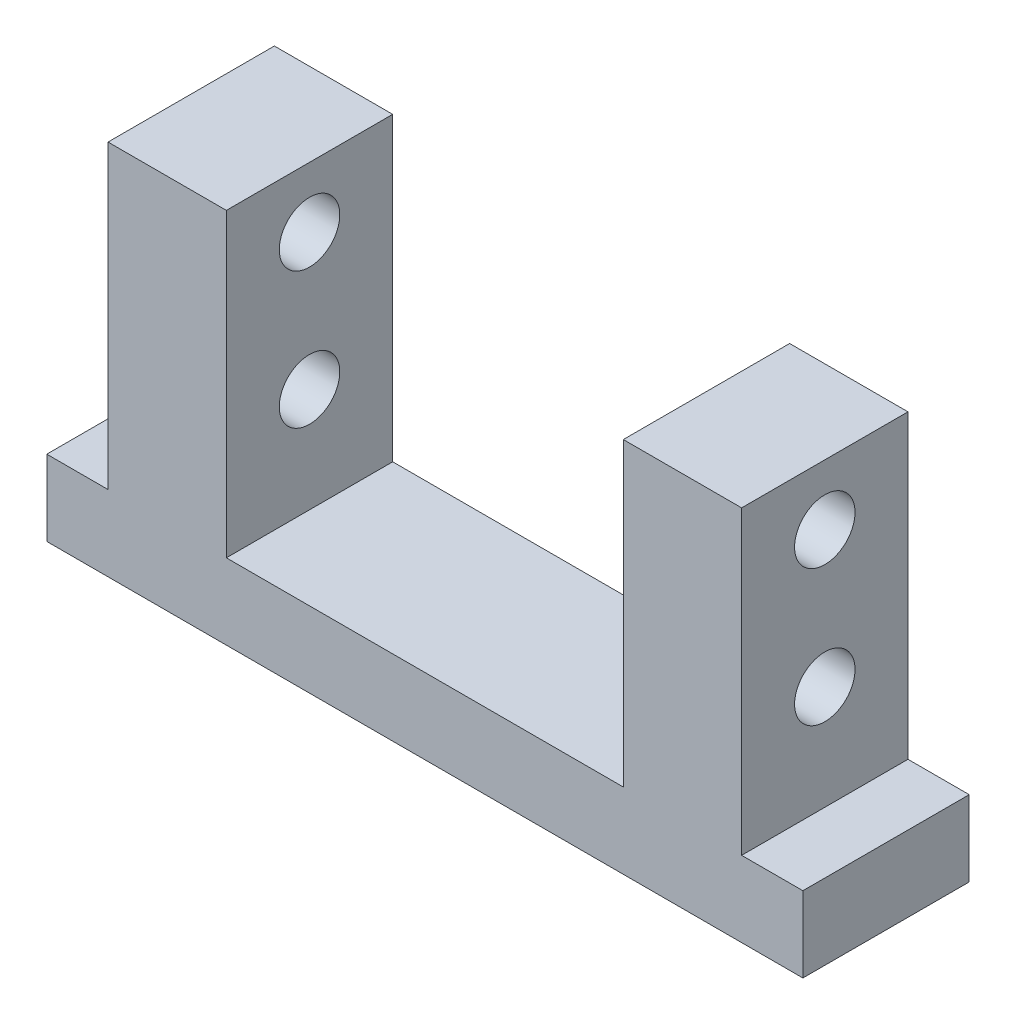
SolidWorks part; units mm, degrees
ref_plane "Front Plane" through (0, 0, 0) normal (0, 0, 1) x (1, 0, 0)
ref_plane "Top Plane" through (0, 0, 0) normal (0, 1, 0) x (1, 0, 0)
ref_plane "Right Plane" through (0, 0, 0) normal (1, 0, 0) x (0, 0, -1)
sketch "Sketch1" plane through (0, 0, 0) normal (0, 1, 0) x (1, 0, 0)
  line L1 (-50, -11) -> (50, -11)
  line L2 (-50, -11) -> (-50, 11)
  line L3 (-50, 11) -> (50, 11)
  line L4 (50, -11) -> (50, 11)
  line L5 (-50, -11) -> (50, 11) construction
  line L6 (-50, 11) -> (50, -11) construction
  point P0 (0, 0)
  dimension "D1" = 100
  dimension "D2" = 22
extrude "Boss-Extrude1" add sketch "Sketch1" along normal blind 10
sketch "Sketch2" plane through (0, 10, 0) normal (0, 1, 0) x (1, 0, 0)
  line L0 (50, 11) -> (-50, 11) construction
  line L1 (41.9, -11) -> (-41.9, -11)
  line L2 (41.9, -11) -> (41.9, 11)
  line L3 (41.9, 11) -> (-41.9, 11)
  line L4 (-41.9, -11) -> (-41.9, 11)
  line L5 (41.9, -11) -> (-41.9, 11) construction
  line L6 (41.9, 11) -> (-41.9, -11) construction
  point P0 (0, 0)
  dimension "D1" = 83.8
extrude "Boss-Extrude2" add sketch "Sketch2" along normal blind 39.8
sketch "Sketch3" plane through (0, 49.8, 0) normal (0, 1, 0) x (1, 0, 0)
  line L0 (41.9, 11) -> (-41.9, 11) construction
  line L1 (26.25, -11) -> (-26.25, -11)
  line L2 (26.25, -11) -> (26.25, 11)
  line L3 (26.25, 11) -> (-26.25, 11)
  line L4 (-26.25, -11) -> (-26.25, 11)
  line L5 (26.25, -11) -> (-26.25, 11) construction
  line L6 (26.25, 11) -> (-26.25, -11) construction
  point P0 (0, 0)
  dimension "D1" = 52.5
extrude "Cut-Extrude1" cut sketch "Sketch3" against normal blind 39.8
sketch "Sketch4" plane through (-41.9, 0, 0) normal (-1, 0, 0) x (0, 0, 1)
  line L0 (-11, 49.8) -> (11, 49.8) construction
  circle A0 centre (0, 41.8) radius 4
  circle A1 centre (0, 23.8) radius 4
  dimension "D3" = 8
  dimension "D4" = 8
  dimension "D1" = 8
  dimension "D2" = 26
extrude "Cut-Extrude2" cut sketch "Sketch4" against normal through all
